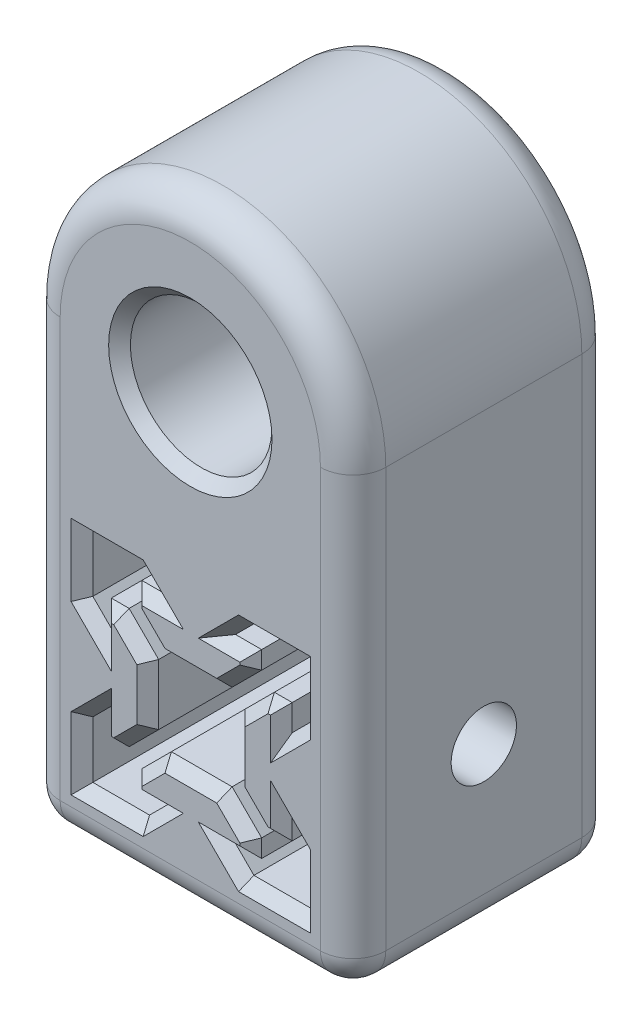
SolidWorks part; units mm, degrees
ref_plane "Front Plane" through (0, 0, 0) normal (0, 0, 1) x (1, 0, 0)
ref_plane "Top Plane" through (0, 0, 0) normal (0, 1, 0) x (1, 0, 0)
ref_plane "Right Plane" through (0, 0, 0) normal (1, 0, 0) x (0, 0, -1)
sketch "Sketch1" plane through (0, 0, 0) normal (0, 0, 1) x (1, 0, 0)
  line L0 (0, -15) -> (0, 15) construction
  line L1 (0, 15) -> (14.8993, 15)
  line L2 (14.8993, 15) -> (14.8993, -14.9496)
  line L3 (14.8993, -14.9496) -> (-15, -14.9496)
  line L4 (-15, -14.9496) -> (-15, 15)
  line L5 (-15, 15) -> (0, 15)
  line L6 (0, -10) -> (0, 10) construction
  line L7 (0, 10) -> (-10, 10) construction
  line L8 (-10, 10) -> (-4.7925, 10)
  line L9 (-4.7925, 10) -> (-3.1, 8.3075)
  line L10 (-3.1, 8.3075) -> (0, 8.3075) construction
  line L11 (-3.1, 8.3075) -> (-5.5, 8.3075)
  line L12 (-5.5, 8.3075) -> (-5.5, 6.6675)
  line L13 (-5.5, 6.6675) -> (-2.79, 3.9575)
  line L14 (-2.79, 3.9575) -> (0, 3.9575) construction
  line L15 (-2.79, 3.9575) -> (2.79, 3.9575)
  line L16 (-10, 10) -> (0, 0) construction
  line L17 (-3.9575, 2.79) -> (-3.9575, -2.79)
  line L18 (-6.6675, 5.5) -> (-3.9575, 2.79)
  line L19 (-8.3075, 5.5) -> (-6.6675, 5.5)
  line L20 (-8.3075, 3.1) -> (-8.3075, 5.5)
  line L21 (-10, 4.7925) -> (-8.3075, 3.1)
  line L22 (-10, 10) -> (-10, 4.7925)
  line L23 (0, 0) -> (-11.0308, 0) construction
  line L24 (5.5, 6.6675) -> (2.79, 3.9575)
  line L25 (5.5, 8.3075) -> (5.5, 6.6675)
  line L26 (3.1, 8.3075) -> (5.5, 8.3075)
  line L27 (4.7925, 10) -> (3.1, 8.3075)
  line L28 (10, 10) -> (4.7925, 10)
  line L29 (10, 10) -> (10, 4.7925)
  line L30 (10, 4.7925) -> (8.3075, 3.1)
  line L31 (8.3075, 3.1) -> (8.3075, 5.5)
  line L32 (8.3075, 5.5) -> (6.6675, 5.5)
  line L33 (6.6675, 5.5) -> (3.9575, 2.79)
  line L34 (3.9575, 2.79) -> (3.9575, -2.79)
  line L35 (-10, -10) -> (0, 0) construction
  line L36 (-2.79, -3.9575) -> (0, -3.9575) construction
  line L37 (-3.1, -8.3075) -> (0, -8.3075) construction
  line L38 (0, -10) -> (-10, -10) construction
  line L39 (6.6675, -5.5) -> (3.9575, -2.79)
  line L40 (8.3075, -5.5) -> (6.6675, -5.5)
  line L41 (8.3075, -3.1) -> (8.3075, -5.5)
  line L42 (10, -4.7925) -> (8.3075, -3.1)
  line L43 (10, -10) -> (10, -4.7925)
  line L44 (10, -10) -> (4.7925, -10)
  line L45 (4.7925, -10) -> (3.1, -8.3075)
  line L46 (3.1, -8.3075) -> (5.5, -8.3075)
  line L47 (5.5, -8.3075) -> (5.5, -6.6675)
  line L48 (5.5, -6.6675) -> (2.79, -3.9575)
  line L49 (-10, -10) -> (-10, -4.7925)
  line L50 (-10, -4.7925) -> (-8.3075, -3.1)
  line L51 (-8.3075, -3.1) -> (-8.3075, -5.5)
  line L52 (-8.3075, -5.5) -> (-6.6675, -5.5)
  line L53 (-6.6675, -5.5) -> (-3.9575, -2.79)
  line L54 (-2.79, -3.9575) -> (2.79, -3.9575)
  line L55 (-5.5, -6.6675) -> (-2.79, -3.9575)
  line L56 (-5.5, -8.3075) -> (-5.5, -6.6675)
  line L57 (-3.1, -8.3075) -> (-5.5, -8.3075)
  line L58 (-4.7925, -10) -> (-3.1, -8.3075)
  line L59 (-10, -10) -> (-4.7925, -10)
  point P43 (3.9575, 0)
  point P58 (-3.9575, 0)
  dimension "D1" = 3.1
  dimension "D2" = 2.79
  dimension "D3" = 2.4
  dimension "D4" = 135
  dimension "D5" = 1.64
  dimension "D6" = 15
  dimension "D7" = 15
  dimension "D8" = 10
  dimension "D9" = 45
extrude "Boss-Extrude1" add sketch "Sketch1" along normal blind 24
sketch "Sketch4" plane through (0, 0, 0) normal (0, 0, -1) x (-1, 0, 0)
  line L0 (0.0504, 15) -> (0.0504, 20) construction
  line L1 (-14.8993, 15) -> (15, 15) construction
  line L2 (0.0504, 20) -> (0.0504, 26.5) construction
  line L3 (-14.8993, 15) -> (-14.8993, 26.5)
  line L4 (15, 26.5) -> (15, 15)
  line L5 (15, 15) -> (-14.8993, 15)
  line L6 (15, -14.9496) -> (-14.8993, -14.9496) construction
  circle A0 centre (0.0504, 26.5) radius 6.5
  arc A1 (-14.8993, 26.5) -> (15, 26.5) centre (0.0504, 26.5) cw
  line M2 (15, 15) -> (-14.8993, 15)
  dimension "D2" = 13
  dimension "D3" = 14.9496
  dimension "D1" = 29.9496
  dimension "D4" = 5
extrude "Boss-Extrude2" add sketch "Sketch4" against normal up to surface (24 mm away) contours A1 L3 L4 A0 M2
sketch "Sketch3" plane through (-15, 0, 0) normal (-1, 0, 0) x (0, 0, 1)
  line L0 (12, 0) -> (24, 5.7752) construction
  line L2 (0, 0) -> (12, 0) construction
  line L3 (24, 26.5) -> (24, -14.9496) construction
  circle A0 centre (12, 0) radius 3
extrude "Cut-Extrude1" cut sketch "Sketch3" against normal through all
fillet "Fillet1" radius 3 10 edges at (-0.0504, -14.9496, 24) (14.8993, 5.7752, 24) (-15, 5.7752, 24) (14.8993, 5.7752, 0) (-15, 5.7752, 0) (-0.0504, -14.9496, 0) (14.8993, -14.9496, 12) (-15, -14.9496, 12) (-0.0504, 41.4496, 24) (-0.0504, 41.4496, 0)
chamfer "Chamfer1" distance 1 angle 45 90 edges at (-6.5504, 26.5, 0) (-4.145, 5.3125, 0) (0, 3.9575, 0) (4.145, 5.3125, 0) (5.5, 7.4875, 0) (4.3, 8.3075, 0) (3.9463, 9.1537, 0) (7.3963, 10, 0) (10, 7.3963, 0) (9.1537, 3.9463, 0) (8.3075, 4.3, 0) (7.4875, 5.5, 0) (5.3125, 4.145, 0) (3.9575, 0, 0) (5.3125, -4.145, 0) (7.4875, -5.5, 0) (8.3075, -4.3, 0) (9.1537, -3.9463, 0) (10, -7.3963, 0) (7.3963, -10, 0) (3.9463, -9.1537, 0) (4.3, -8.3075, 0) (5.5, -7.4875, 0) (4.145, -5.3125, 0) (0, -3.9575, 0) (-4.145, -5.3125, 0) (-5.5, -7.4875, 0) (-4.3, -8.3075, 0) (-3.9463, -9.1537, 0) (-7.3963, -10, 0) (-10, -7.3963, 0) (-9.1537, -3.9463, 0) (-8.3075, -4.3, 0) (-7.4875, -5.5, 0) (-5.3125, -4.145, 0) (-3.9575, 0, 0) (-5.3125, 4.145, 0) (-7.4875, 5.5, 0) (-8.3075, 4.3, 0) (-9.1537, 3.9463, 0) (-10, 7.3963, 0) (-7.3963, 10, 0) (-3.9463, 9.1537, 0) (-4.3, 8.3075, 0) (-5.5, 7.4875, 0) (-6.5504, 26.5, 24) (-3.9463, 9.1537, 24) (-7.3963, 10, 24) (-10, 7.3963, 24) (-9.1537, 3.9463, 24) (-8.3075, 4.3, 24) (-7.4875, 5.5, 24) (-5.3125, 4.145, 24) (-3.9575, 0, 24) (-5.3125, -4.145, 24) (-7.4875, -5.5, 24) (-8.3075, -4.3, 24) (-9.1537, -3.9463, 24) (-10, -7.3963, 24) (-7.3963, -10, 24) (-3.9463, -9.1537, 24) (-4.3, -8.3075, 24) (-5.5, -7.4875, 24) (-4.145, -5.3125, 24) (0, -3.9575, 24) (4.145, -5.3125, 24) (5.5, -7.4875, 24) (4.3, -8.3075, 24) (3.9463, -9.1537, 24) (7.3963, -10, 24) (10, -7.3963, 24) (9.1537, -3.9463, 24) (8.3075, -4.3, 24) (7.4875, -5.5, 24) (5.3125, -4.145, 24) (3.9575, 0, 24) (5.3125, 4.145, 24) (7.4875, 5.5, 24) (8.3075, 4.3, 24) (9.1537, 3.9463, 24) (10, 7.3963, 24) (7.3963, 10, 24) (3.9463, 9.1537, 24) (4.3, 8.3075, 24) (5.5, 7.4875, 24) (4.145, 5.3125, 24) (0, 3.9575, 24) (-4.145, 5.3125, 24) (-5.5, 7.4875, 24) (-4.3, 8.3075, 24)
